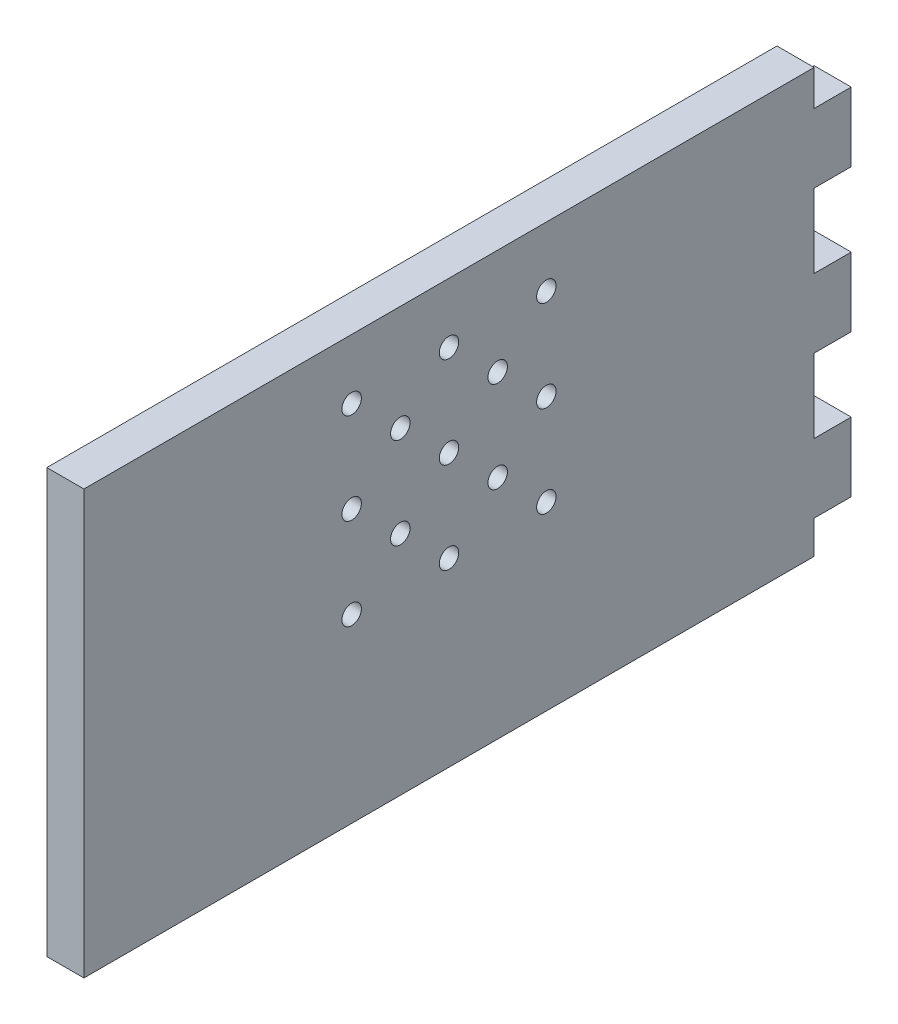
SolidWorks part; units mm, degrees
ref_plane "Plan de face" through (0, 0, 0) normal (0, 0, 1) x (1, 0, 0)
ref_plane "Plan de dessus" through (0, 0, 0) normal (0, 1, 0) x (1, 0, 0)
ref_plane "Plan de droite" through (0, 0, 0) normal (1, 0, 0) x (0, 0, -1)
sketch "Esquisse1" plane through (0, 0, 0) normal (0, 0, 1) x (1, 0, 0)
  line L0 (465.25, 67.8853) -> (465.25, 38.5282) construction
  line L1 (465.25, 170.0639) -> (450, 170.0639)
  line L2 (465.25, 170.0639) -> (465.25, -3.9361)
  line L3 (465.25, -3.9361) -> (450, -3.9361)
  line L4 (450, 170.0639) -> (450, -3.9361)
  line L5 (330.25, 170.0639) -> (315.25, 170.0639) construction
  line L7 (2.0026, -3.9361) -> (465.25, -3.9361) construction
  dimension "D1" = 15.25
extrude "Boss.-Extru.1" add sketch "Esquisse1" along normal up to surface (300 mm away)
sketch "Esquisse2" plane through (465.25, 0, 0) normal (1, 0, 0) x (0, 0, -1)
  line L0 (0, -3.9361) -> (0, 170.0639) construction
  line L1 (0, 155.4567) -> (15.25, 155.4567)
  line L2 (0, 155.4567) -> (0, 127.0996)
  line L3 (0, 127.0996) -> (15.25, 127.0996)
  line L4 (15.25, 155.4567) -> (15.25, 127.0996)
  line L5 (0, 126.5996) -> (15.25, 126.5996) construction
  line L6 (0, 96.7424) -> (15.25, 96.7424)
  line L7 (0, 96.7424) -> (0, 68.3853)
  line L8 (0, 68.3853) -> (15.25, 68.3853)
  line L9 (15.25, 96.7424) -> (15.25, 68.3853)
  line L10 (0, 38.0282) -> (15.25, 38.0282)
  line L11 (0, 38.0282) -> (0, 9.671)
  line L12 (0, 9.671) -> (15.25, 9.671)
  line L13 (15.25, 38.0282) -> (15.25, 9.671)
  line L14 (0, 127.0996) -> (0, 96.7424) construction
  line L15 (0, 68.3853) -> (0, 38.0282) construction
  line L16 (0, 9.171) -> (15.25, 9.171) construction
  line L17 (0, 155.9567) -> (15.25, 155.9567) construction
  dimension "D1" = 0.5
  dimension "D2" = 0.5
  dimension "D3" = 0.5
extrude "Boss.-Extru.2" add sketch "Esquisse2" against normal blind 15.25
sketch "Esquisse3" plane through (465.25, 0, 0) normal (1, 0, 0) x (0, 0, -1)
  line L0 (-150, 145.4567) -> (-150, 70.4567) construction
  line L1 (-110, 145.4567) -> (-190, 145.4567) construction
  line L2 (-110, 145.4567) -> (-110, 70.4567) construction
  line L3 (-110, 70.4567) -> (-190, 70.4567) construction
  line L4 (-190, 145.4567) -> (-190, 70.4567) construction
  line L5 (-110, 107.9567) -> (-190, 107.9567) construction
  line L6 (-300, -3.9361) -> (0, -3.9361) construction
  line L7 (-150, -3.9361) -> (-150, 170.0639) construction
  line L8 (-300, 170.0639) -> (0, 170.0639) construction
  line L9 (-190, 145.4567) -> (-110, 70.4567) construction
  line L10 (-150, 145.4567) -> (-110, 107.9567) construction
  line L11 (-190, 107.9567) -> (-150, 70.4567) construction
  line L12 (-150, 145.4567) -> (-190, 107.9567) construction
  line L13 (-110, 145.4567) -> (-190, 70.4567) construction
  line L14 (-110, 107.9567) -> (-150, 70.4567) construction
  line L15 (15.25, 155.4567) -> (0, 155.4567) construction
  circle A0 centre (-110, 145.4567) radius 4
  circle A2 centre (-110, 70.4567) radius 4
  circle A3 centre (-150, 70.4567) radius 4
  circle A5 centre (-150, 145.4567) radius 4
  circle A6 centre (-190, 145.4567) radius 4
  circle A8 centre (-190, 70.4567) radius 4
  circle A9 centre (-130, 126.7067) radius 4
  circle A10 centre (-170, 126.7067) radius 4
  circle A11 centre (-190, 107.9567) radius 4
  circle A12 centre (-170, 89.2067) radius 4
  circle A13 centre (-130, 89.2067) radius 4
  circle A14 centre (-110, 107.9567) radius 4
  circle A15 centre (-150, 107.9567) radius 4
  point P34 (-130, 89.2067)
  dimension "D1" = 8
  dimension "D2" = 80
  dimension "D3" = 10
  dimension "D4" = 75
extrude "Enlèv. mat.-Extru.1" cut sketch "Esquisse3" against normal up to next
